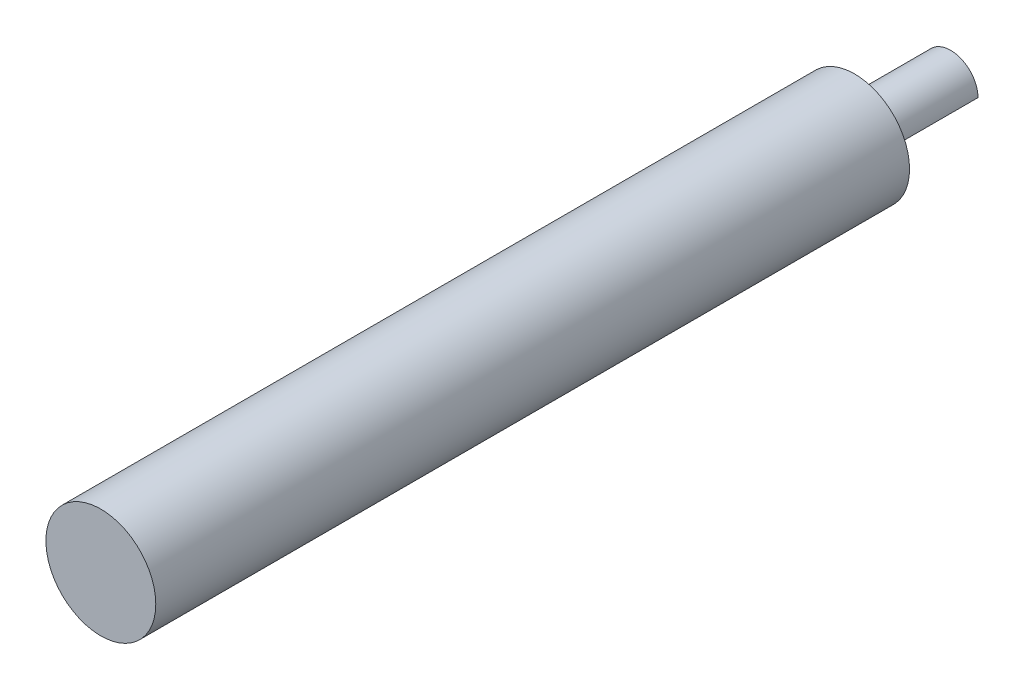
SolidWorks part; units mm, degrees
material "AISI 1020"
ref_plane "Front Plane" through (0, 0, 0) normal (0, 0, 1) x (1, 0, 0)
ref_plane "Top Plane" through (0, 0, 0) normal (0, 1, 0) x (1, 0, 0)
ref_plane "Right Plane" through (0, 0, 0) normal (1, 0, 0) x (0, 0, -1)
sketch "Sketch1" plane through (0, 0, 0) normal (0, 0, 1) x (1, 0, 0)
  circle A0 centre (0, 0) radius 3.1623
  dimension "D1" = 6.3246
extrude "Boss-Extrude1" add sketch "Sketch1" along normal blind 11.0998
sketch "Sketch2" plane through (0, 0, 0) normal (0, 0, -1) x (-1, 0, 0)
  line L0 (0.0012, -3.1623) -> (-3.1623, 0.0012)
  circle A0 centre (0, 0) radius 3.1623 construction
  dimension "D1" = 2.2352
extrude "Cut-Extrude1" cut sketch "Sketch2" against normal through all and the other way through all
sketch "Sketch3" plane through (0, 0, 11.0998) normal (0, 0, 1) x (1, 0, 0)
  circle A0 centre (0, 0) radius 6.35
  dimension "D1" = 12.7
extrude "Boss-Extrude2" add sketch "Sketch3" along normal blind 87.122
sketch "Sketch5" plane through (0, 0, 98.2218) normal (0, 0, 1) x (1, 0, 0)
  circle A0 centre (0, 0) radius 6.35
fillet "Fillet1" [suppressed] radius 1.27
